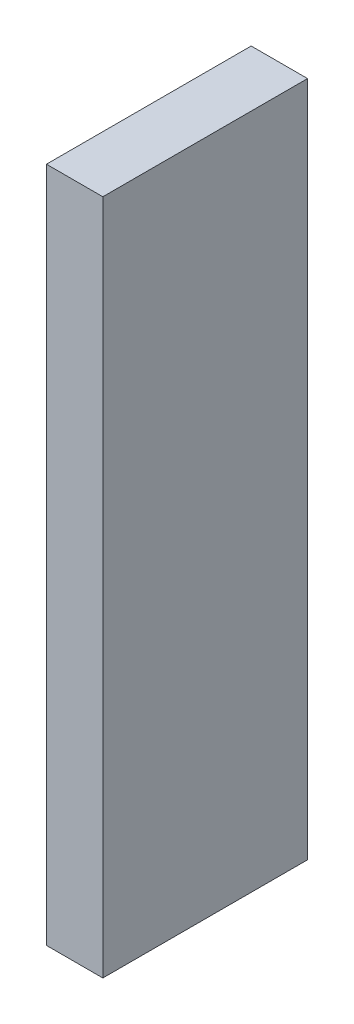
SolidWorks part; units mm, degrees
ref_plane "Front Plane" through (0, 0, 0) normal (0, 0, 1) x (1, 0, 0)
ref_plane "Top Plane" through (0, 0, 0) normal (0, 1, 0) x (1, 0, 0)
ref_plane "Right Plane" through (0, 0, 0) normal (1, 0, 0) x (0, 0, -1)
ref_plane "Plane1" through (675, 0, 0) normal (1, 0, 0) x (0, 0, -1)
sketch "Sketch1" plane through (675, 0, 0) normal (1, 0, 0) x (0, 0, -1)
  line L1 (-7.256, 923.2157) -> (-1.8099, 923.2157)
  line L2 (-7.256, 923.2157) -> (-7.256, 905.2174)
  line L3 (-7.256, 905.2174) -> (-1.8099, 905.2174)
  line L4 (-1.8099, 923.2157) -> (-1.8099, 905.2174)
extrude "Boss-Extrude1" add sketch "Sketch1" against normal blind 1.5
